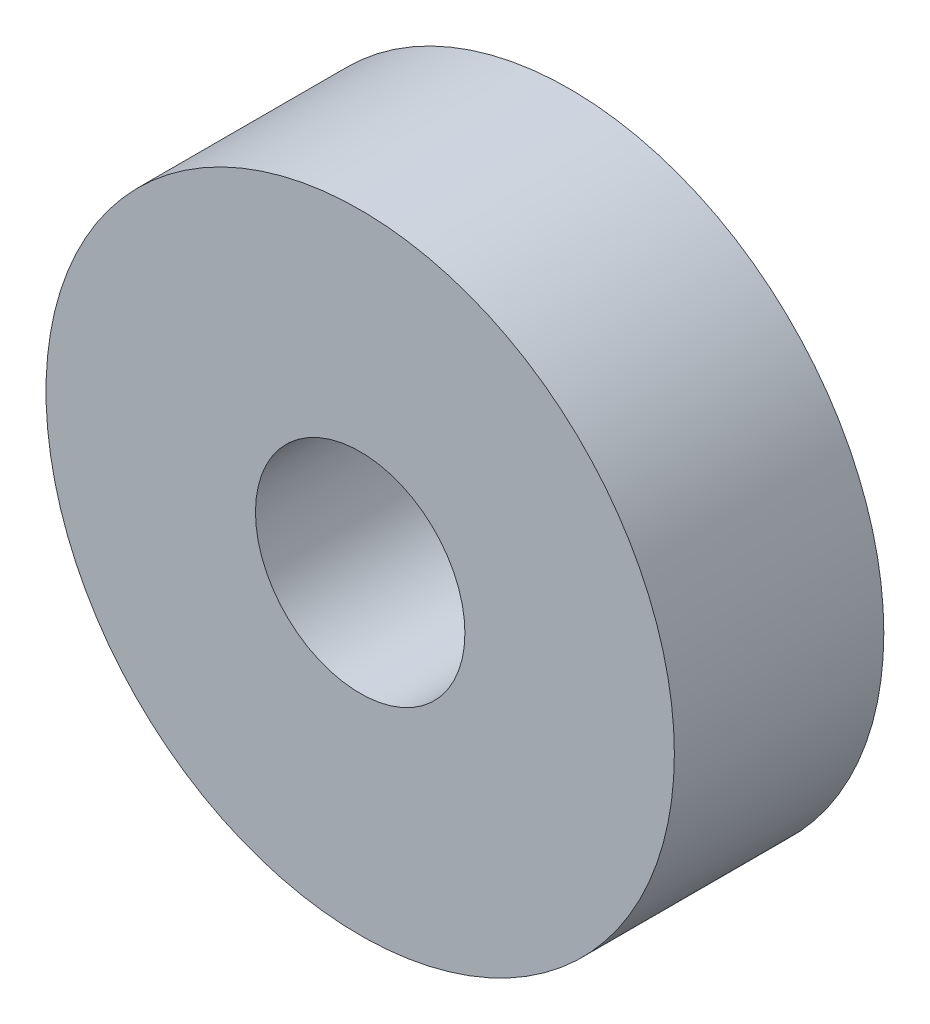
SolidWorks part; units mm, degrees
material "Cast Alloy Steel"
ref_plane "Front Plane" through (0, 0, 0) normal (0, 0, 1) x (1, 0, 0)
ref_plane "Top Plane" through (0, 0, 0) normal (0, 1, 0) x (1, 0, 0)
ref_plane "Right Plane" through (0, 0, 0) normal (1, 0, 0) x (0, 0, -1)
sketch "Sketch1" plane through (0, 0, 0) normal (0, 0, 1) x (1, 0, 0)
  circle A0 centre (0, 0) radius 14.25
  circle A1 centre (0, 0) radius 4.75
  dimension "D1" = 28.5
  dimension "D2" = 9.5
extrude "Boss-Extrude1" add sketch "Sketch1" along normal mid plane 9.5
